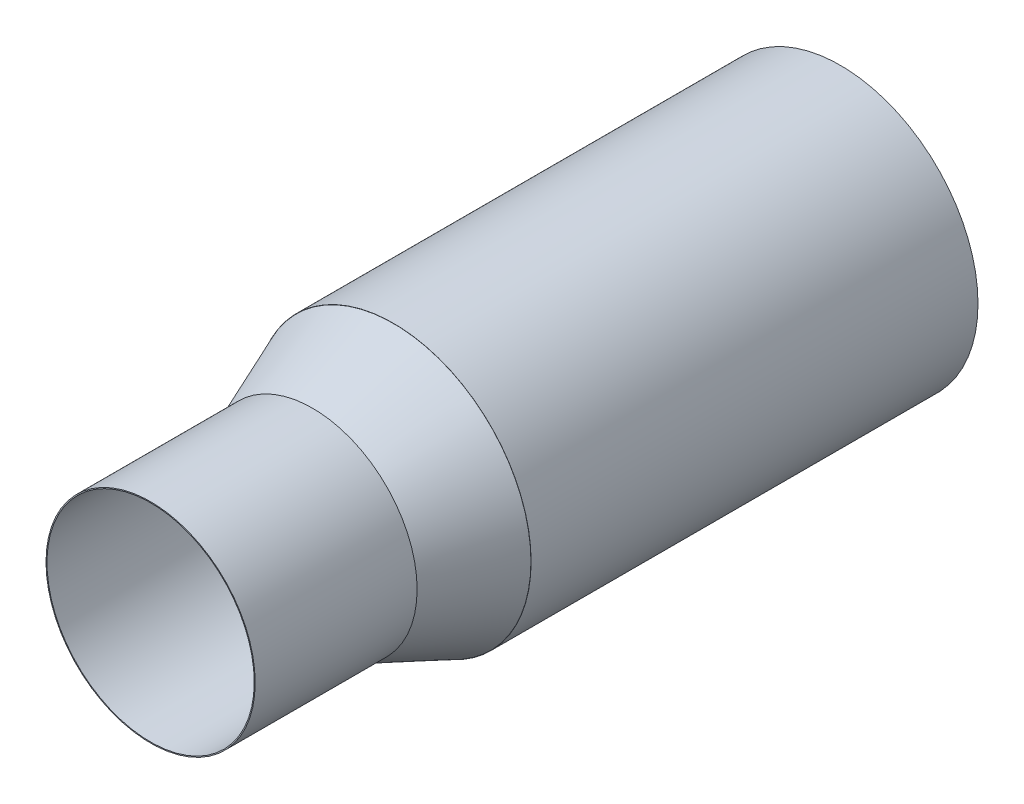
SolidWorks part; units mm, degrees
ref_plane "Front Plane" through (0, 0, 0) normal (0, 0, 1) x (1, 0, 0)
ref_plane "Top Plane" through (0, 0, 0) normal (0, 1, 0) x (1, 0, 0)
ref_plane "Right Plane" through (0, 0, 0) normal (1, 0, 0) x (0, 0, -1)
sketch "Sketch1" plane through (0, 0, 0) normal (0, 0, 1) x (1, 0, 0)
  line L0 (0, 0) -> (-20.1218, 11.3741) construction
  line L1 (0, 0) -> (19.9112, 11.7389) construction
  line L2 (0, 0) -> (0.2377, -23.114) construction
  circle A4 centre (0.1189, -11.557) radius 9.144
  circle A5 centre (9.9556, 5.8695) radius 9.144
  circle A6 centre (-10.0609, 5.687) radius 9.144
  circle A8 centre (0, 0) radius 21.59
  point P1 (2.188, 1.29)
  point P2 (-2.2112, 1.2499)
  point P6 (0.0261, -2.54)
  point P7 (9.9556, 5.8695)
  point P8 (-10.0609, 5.687)
  point P9 (0.1189, -11.557)
  dimension "D1" = 2.54
  dimension "D2" = 2.54
  dimension "D3" = 2.54
  dimension "D4" = 9.017
  dimension "D5" = 9.017
  dimension "D6" = 9.017
extrude "Boss-Extrude1" add sketch "Sketch1" along normal blind 70.1
sketch "Sketch2" plane through (0, 0, 70.1) normal (0, 0, 1) x (1, 0, 0)
  circle A0 centre (0, 0) radius 21.59
  circle A2 centre (0, 0) radius 16.4084
  circle A3 centre (0, 0) radius 16.256
  circle M4 centre (9.9556, 5.8695) radius 9.144
  circle M6 centre (0.1189, -11.557) radius 9.144
  circle M7 centre (-10.0609, 5.687) radius 9.144
extrude "Boss-Extrude2" add sketch "Sketch2" along normal blind 38.1 contours A3 A2 M7 | A3 A2 M4 M7 | A3 A2 M4 | A3 A2 M6 M4 | A3 A2 M6 | A3 A2 M7 M6
sketch "Sketch8" plane through (0, 0, 0) normal (1, 0, 0) x (0, 0, -1)
  line L0 (-126.1598, 0) -> (24.1508, 0) construction
  line L1 (-70.1, -0.6209) -> (-70.1, 31.6682) construction
  line L2 (-89.15, 16.4084) -> (-70.1, 16.4084) construction
  line L3 (-70.1, 16.4084) -> (-108.2, 16.4084) construction
  line L4 (-70.1, 21.5623) -> (-82.8, 16.4084)
  line L5 (-70.1, 21.5623) -> (-70.1, 16.4084)
  line L6 (-70.1, 16.4084) -> (-82.8, 16.4084)
  point P10 (-82.8, 16.4084)
  dimension "D1" = 12.7
revolve "Revolve3" add sketch "Sketch8" angle 360 about L0
